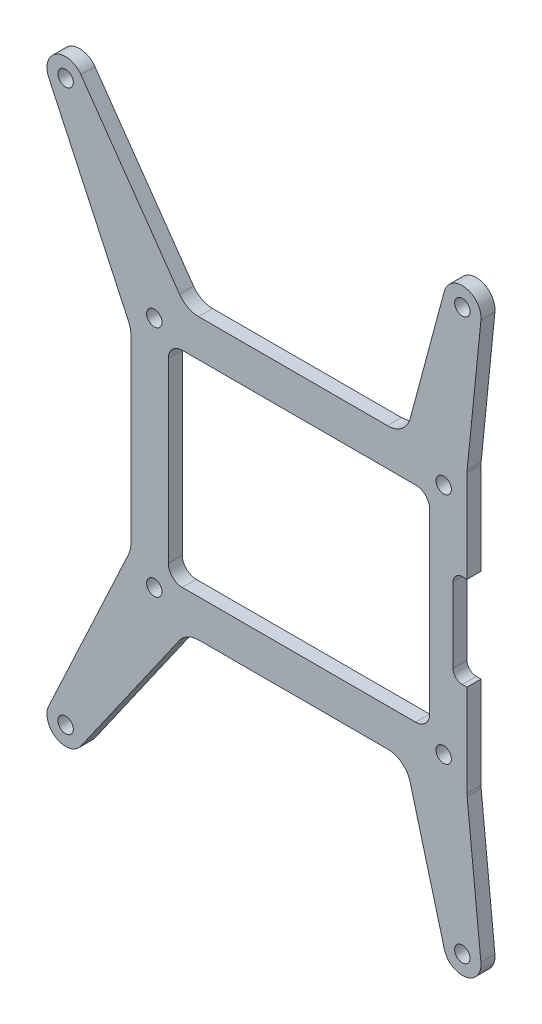
SolidWorks part; units mm, degrees
material "A-玻璃纤维"
ref_plane "前视基准面" through (0, 0, 0) normal (0, 0, 1) x (1, 0, 0)
ref_plane "上视基准面" through (0, 0, 0) normal (0, 1, 0) x (1, 0, 0)
ref_plane "右视基准面" through (0, 0, 0) normal (1, 0, 0) x (0, 0, -1)
sketch "草图1" plane through (0, 0, 0) normal (0, 0, 1) x (1, 0, 0)
  line L0 (-36, 30) -> (36, 30)
  line L1 (-31, 25) -> (31, 25) construction
  line L2 (-31, 25) -> (-31, -25) construction
  line L3 (-31, -25) -> (31, -25) construction
  line L4 (31, 25) -> (31, -25) construction
  line L5 (-31, 25) -> (31, -25) construction
  line L6 (-31, -25) -> (31, 25) construction
  line L7 (36, 30) -> (36, -30)
  line L8 (-36, -30) -> (36, -30)
  line L9 (-36, 30) -> (-36, -30)
  line L10 (-28, 22) -> (28, 22)
  line L11 (28, 22) -> (28, -22)
  line L12 (-28, -22) -> (28, -22)
  line L13 (-28, 22) -> (-28, -22)
  circle A0 centre (31, -25) radius 1.65
  circle A1 centre (31, 25) radius 1.65
  circle A2 centre (-31, 25) radius 1.65
  circle A3 centre (-31, -25) radius 1.65
  point P0 (0, 0)
  dimension "D3" = 3.3
  dimension "D1" = 62
  dimension "D2" = 50
  dimension "D4" = 5
  dimension "D5" = 3
extrude "凸台-拉伸1" add sketch "草图1" along normal blind 3
fillet "圆角1" radius 3 4 edges at (-28, 22, 1.5) (28, 22, 1.5) (28, -22, 1.5) (-28, -22, 1.5)
sketch "草图2" plane through (0, 0, 3) normal (0, 0, 1) x (1, 0, 0)
  line L0 (0, 0) -> (-91.1285, 0) construction
  line L1 (0, 0) -> (0, 64.8036) construction
  line L2 (-46.7234, 62.2943) -> (-24.1107, 30)
  line L3 (36, 30) -> (-36, 30) construction
  line L7 (-46.7234, -62.2943) -> (-24.1107, -30)
  line L8 (-24.1107, 30) -> (-36, 30)
  line L9 (0, 60) -> (35, 60) construction
  line L18 (31.1363, 61.0353) -> (22.8204, 30)
  line L19 (38.9799, 59.5993) -> (36, 30)
  line L20 (36, -30) -> (36, 30) construction
  line L21 (38.9799, -59.5993) -> (36, -30)
  line L22 (31.1363, -61.0353) -> (22.8204, -30)
  line L23 (-36, -30) -> (36, -30) construction
  line L24 (22.8204, -30) -> (36, -30)
  line L26 (-36, 30) -> (-36, -30)
  line L27 (-36, -30) -> (36, -30)
  line L28 (36, -30) -> (36, 30)
  line L29 (36, 30) -> (-36, 30)
  line L31 (-36, -30) -> (-24.1107, -30)
  line L33 (36, 30) -> (22.8204, 30)
  line L34 (36, -30) -> (36, 30) construction
  line L35 (-36, -30) -> (36, -30) construction
  line L36 (-53.6252, -58.3095) -> (-36, -20.5121)
  line L37 (-36, 30) -> (-36, -30) construction
  line L38 (-53.6252, 58.3095) -> (-36, 20.5121)
  line L39 (-36, 30) -> (-36, 20.5121)
  line L40 (-36, -20.5121) -> (-36, -30)
  circle A0 centre (-50, 60) radius 1.65
  circle A1 centre (-50, -60) radius 1.65
  arc A2 (-46.7234, 62.2943) -> (-53.6252, 58.3095) centre (-50, 60) ccw
  arc A3 (-46.7234, -62.2943) -> (-53.6252, -58.3095) centre (-50, -60) cw
  circle A4 centre (35, 60) radius 1.65
  arc A5 (38.9799, 59.5993) -> (31.1363, 61.0353) centre (35, 60) ccw
  circle A6 centre (35, -60) radius 1.65
  arc A7 (38.9799, -59.5993) -> (31.1363, -61.0353) centre (35, -60) cw
  dimension "D1" = 3.3
  dimension "D2" = 8
  dimension "D3" = 120
  dimension "D6" = 3.3
  dimension "D7" = 8
  dimension "D5" = 60
  dimension "D8" = 35
  dimension "D9" = 50
  dimension "D10" = 105
  dimension "D11" = 125
  dimension "D12" = 155
  dimension "D4" = 0
extrude "凸台-拉伸2" add sketch "草图2" against normal blind 3
fillet "圆角2" radius 5 6 edges at (22.8204, -30, 1.5) (-24.1107, -30, 1.5) (22.8204, 30, 1.5) (-24.1107, 30, 1.5) (36, -30, 1.5) (36, 30, 1.5)
fillet "圆角3" radius 6 2 edges at (-36, 20.5121, 1.5) (-36, -20.5121, 1.5)
sketch "草图3" plane through (0, 0, 3) normal (0, 0, 1) x (1, 0, 0)
  line L0 (0, 0) -> (56.8073, 0) construction
  line L1 (36, -29.7489) -> (36, 29.7489) construction
  line L2 (36, -29.7489) -> (36, 29.7489) construction
  line L4 (39, -10) -> (33, -10)
  line L5 (39, -10) -> (39, 10)
  line L6 (39, 10) -> (33, 10)
  line L7 (33, -10) -> (33, 10)
  line L8 (39, -10) -> (33, 10) construction
  line L9 (39, 10) -> (33, -10) construction
  point P5 (36, 0)
  dimension "D1" = 6
  dimension "D2" = 20
extrude "切除-拉伸1" cut sketch "草图3" against normal through all
fillet "圆角4" radius 2 2 edges at (33, 10, 1.5) (33, -10, 1.5)
